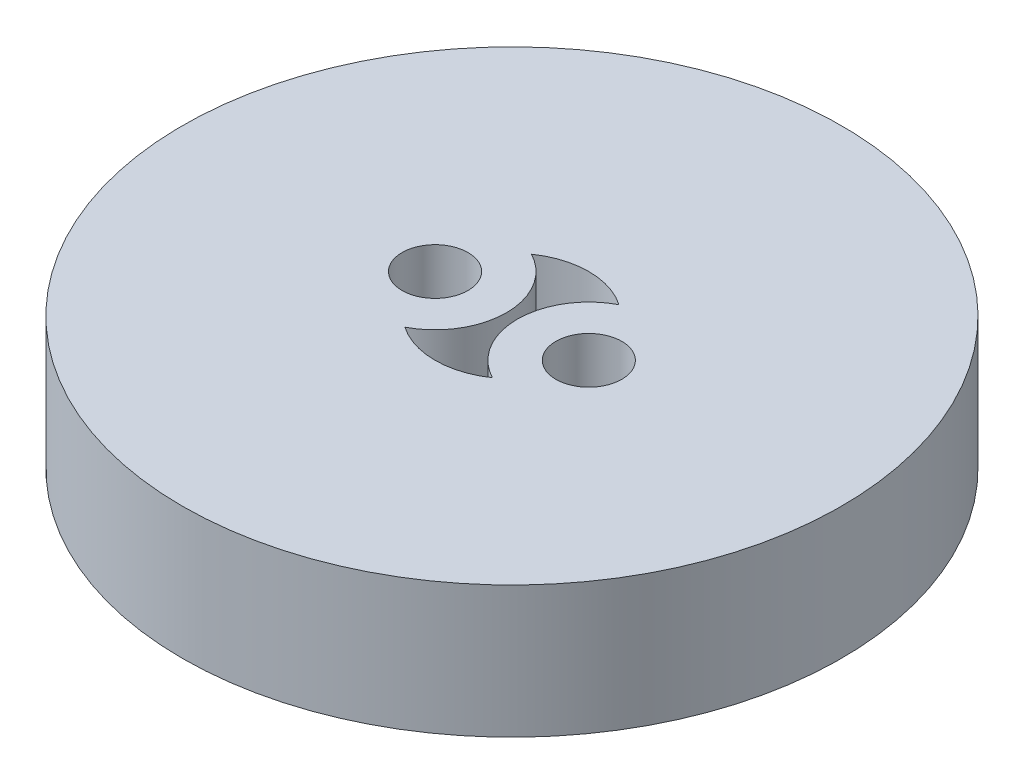
SolidWorks part; units mm, degrees
ref_plane "Plan de face" through (0, 0, 0) normal (0, 0, 1) x (1, 0, 0)
ref_plane "Plan de dessus" through (0, 0, 0) normal (0, 1, 0) x (1, 0, 0)
ref_plane "Plan de droite" through (0, 0, 0) normal (1, 0, 0) x (0, 0, -1)
sketch "Esquisse1" plane through (0, 0, 0) normal (0, 1, 0) x (1, 0, 0)
  line L0 (-3.5, 0) -> (3.5, 0) construction
  circle A0 centre (0, 0) radius 15
  circle A2 centre (-3.5, 0) radius 1.5
  circle A3 centre (3.5, 0) radius 1.5
  arc A4 (1.9911, 2.8785) -> (1.9911, -2.8785) centre (3.5, 0) ccw
  arc A5 (-1.9911, -2.8785) -> (-1.9911, 2.8785) centre (-3.5, 0) ccw
  arc A6 (-1.9911, -2.8785) -> (1.9911, -2.8785) centre (0, 0) ccw
  arc A9 (1.9911, 2.8785) -> (-1.9911, 2.8785) centre (0, 0) ccw
  circle A10 centre (-3.5, 0) radius 3.25 construction
  circle A11 centre (3.5, 0) radius 3.25 construction
  dimension "D1" = 30
  dimension "D2" = 6.5
  dimension "D3" = 6.5
  dimension "D4" = 7
  dimension "D5" = 3
  dimension "D6" = 3
  dimension "D7" = 3.5
  dimension "D8" = 3.5
  dimension "D9" = 3.25
  dimension "D10" = 3.25
  dimension "D11" = 3.5
extrude "Boss.-Extru.1" add sketch "Esquisse1" along normal blind 6
